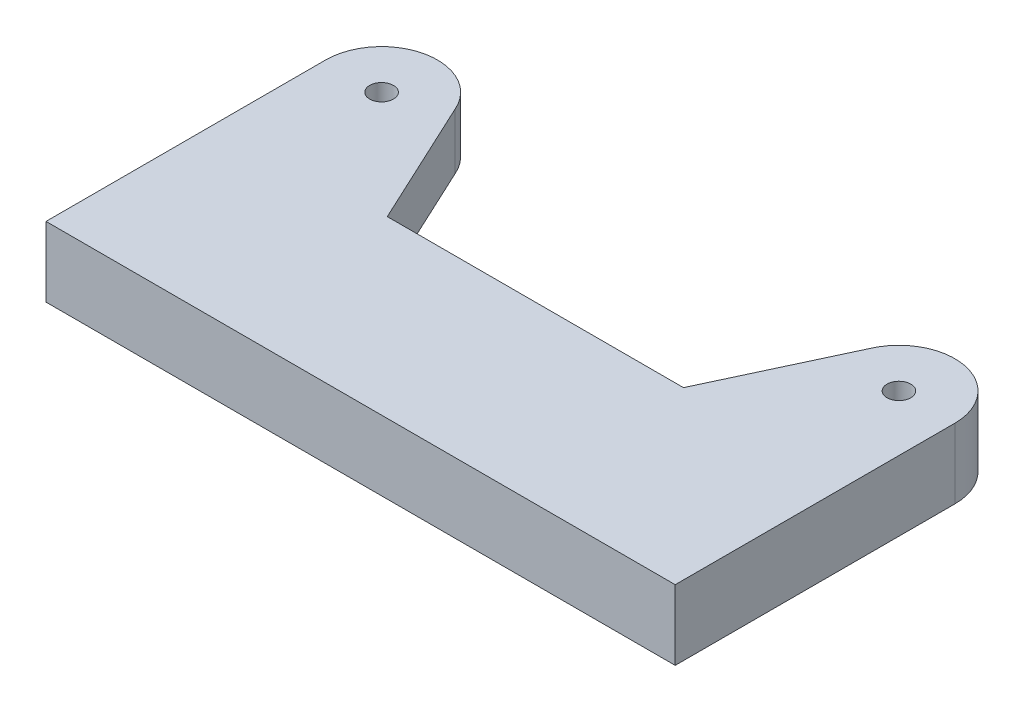
SolidWorks part; units mm, degrees
ref_plane "Front Plane" through (0, 0, 0) normal (0, 0, 1) x (1, 0, 0)
ref_plane "Top Plane" through (0, 0, 0) normal (0, 1, 0) x (1, 0, 0)
ref_plane "Right Plane" through (0, 0, 0) normal (1, 0, 0) x (0, 0, -1)
sketch "Sketch1" plane through (0, 0, 0) normal (0, 1, 0) x (1, 0, 0)
  line L0 (45, 0) -> (-45, 0)
  line L1 (0, 0) -> (0, 31.9541) construction
  line L2 (45, 0) -> (45, 40)
  line L3 (29.6361, 43.1262) -> (21.1837, 25)
  line L4 (21.1837, 25) -> (-21.1837, 25)
  line L5 (-29.6361, 43.1262) -> (-21.1837, 25)
  line L6 (-45, 0) -> (-45, 40)
  arc A0 (45, 40) -> (29.6361, 43.1262) centre (37, 40) ccw
  arc A1 (-45, 40) -> (-29.6361, 43.1262) centre (-37, 40) cw
  point P0 (-30.387, 44.502)
  point P15 (0, 25)
  dimension "D2" = 8
  dimension "D1" = 90
  dimension "D3" = 25
  dimension "D4" = 115
  dimension "D5" = 40
  dimension "D6" = 20
extrude "Boss-Extrude1" add sketch "Sketch1" along normal blind 10
sketch "Sketch2" plane through (0, 0, 0) normal (0, -1, 0) x (1, 0, 0)
  line L0 (-45, 0) -> (45, 0) construction
  line L1 (42.5, -48) -> (-42.5, -48)
  line L2 (42.5, -48) -> (42.5, -15)
  line L3 (42.5, -15) -> (-42.5, -15)
  line L4 (-42.5, -48) -> (-42.5, -15)
  line L5 (42.5, -48) -> (-42.5, -15) construction
  line L6 (42.5, -15) -> (-42.5, -48) construction
  arc A0 (29.6361, -43.1262) -> (45, -40) centre (37, -40) ccw construction
  point P0 (0, -31.5)
  point P5 (0, -32.8158)
  point P9 (0, 0)
  dimension "D1" = 85
  dimension "D2" = 15
extrude "Cut-Extrude1" cut sketch "Sketch2" against normal blind 2
fillet "Fillet1" radius 1 2 edges at (-42.5, 1, -15) (42.5, 1, -15)
hole_wizard "M3 Clearance Hole1" positions "Sketch3" profile "Sketch4" hole size "M3" standard "ANSI Metric"
sketch "Sketch3" plane through (0, 10, 0) normal (0, 1, 0) x (1, 0, 0)
  point P0 (-37, 40)
  point P2 (37, 40)
sketch "Sketch4" plane through (-37, 10, -40) normal (1, 0, 0) x (0, 0, 1)
  line L0 (0, 0) -> (0, 9.0215)
  line L1 (0, 9.0215) -> (1.7, 8)
  line L2 (1.7, 8) -> (1.7, 0)
  line L5 (1.7, 0) -> (0, 0)
  line L10 (0, 9.0215) -> (-1.7, 8) construction
  line L11 (0, -6.35) -> (0, 107.95) construction
  dimension "Hole Dia." = 3.4
  dimension "Hole Depth" = 8
  dimension "Drill Angle" = 118
